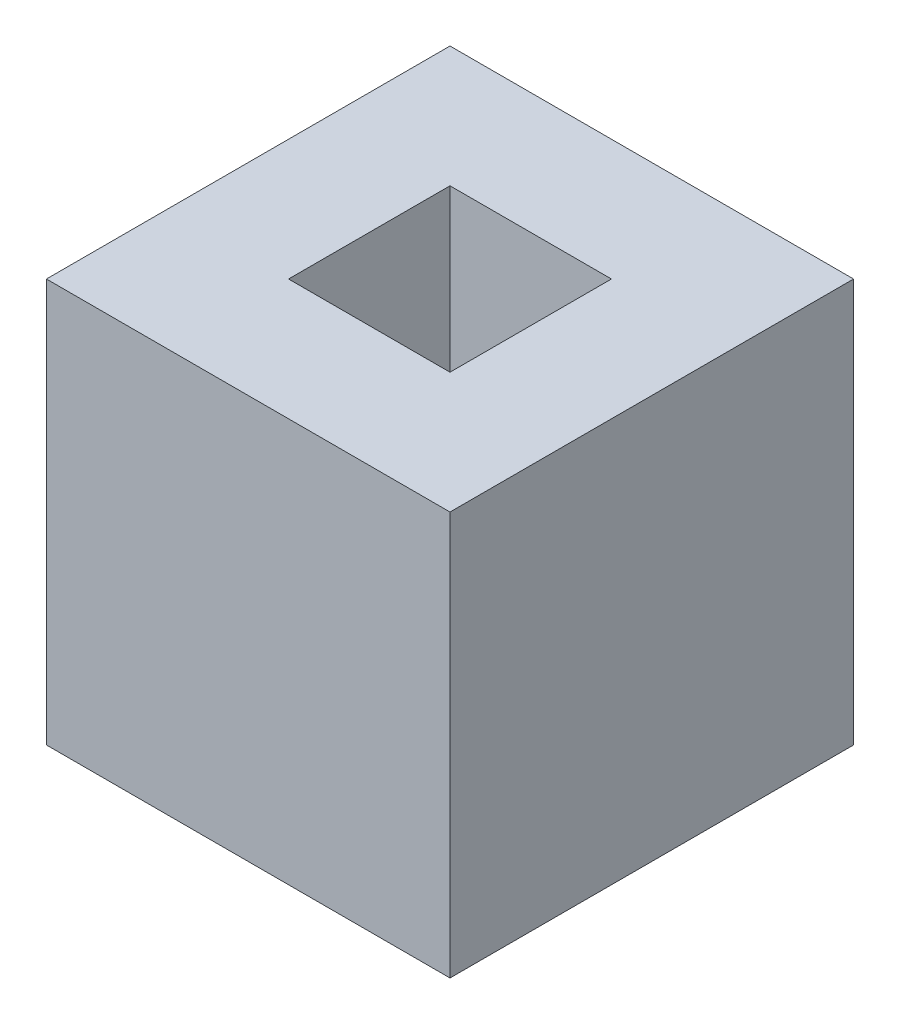
SolidWorks part; units mm, degrees
ref_plane "Front Plane" through (0, 0, 0) normal (0, 0, 1) x (1, 0, 0)
ref_plane "Top Plane" through (0, 0, 0) normal (0, 1, 0) x (1, 0, 0)
ref_plane "Right Plane" through (0, 0, 0) normal (1, 0, 0) x (0, 0, -1)
sketch "Sketch1" plane through (0, 0, 0) normal (0, 1, 0) x (1, 0, 0)
  line L1 (0, 10) -> (10, 10)
  line L2 (0, 10) -> (0, 0)
  line L3 (0, 0) -> (10, 0)
  line L4 (10, 10) -> (10, 0)
  dimension "D1" = 10
  dimension "D2" = 10
extrude "Boss-Extrude1" add sketch "Sketch1" along normal blind 10
sketch "Sketch2" plane through (0, 10, 0) normal (0, 1, 0) x (1, 0, 0)
  line L0 (10, 0) -> (10, 10) construction
  line L1 (7, 7) -> (3, 7)
  line L2 (7, 7) -> (7, 3)
  line L3 (7, 3) -> (3, 3)
  line L4 (3, 7) -> (3, 3)
  line L5 (0, 10) -> (0, 0) construction
  line L6 (0, 0) -> (10, 0) construction
  line L7 (10, 10) -> (0, 10) construction
  dimension "D1" = 3
  dimension "D2" = 3
  dimension "D3" = 3
  dimension "D4" = 3
extrude "Cut-Extrude1" cut sketch "Sketch2" against normal through all
